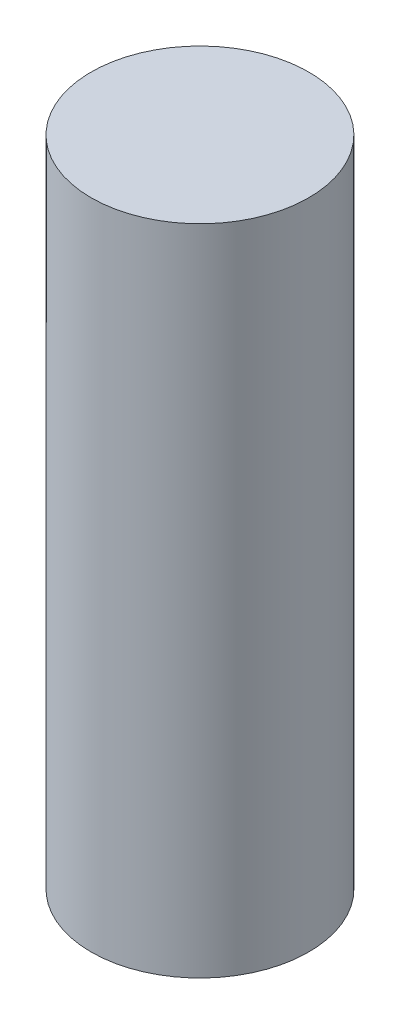
SolidWorks part; units mm, degrees
ref_plane "前视基准面" through (0, 0, 0) normal (0, 0, 1) x (1, 0, 0)
ref_plane "上视基准面" through (0, 0, 0) normal (0, 1, 0) x (1, 0, 0)
ref_plane "右视基准面" through (0, 0, 0) normal (1, 0, 0) x (0, 0, -1)
sketch "草图1" plane through (0, 0, 0) normal (0, 1, 0) x (1, 0, 0)
  circle A0 centre (0, 0) radius 2.5
  dimension "D1" = 5
extrude "凸台-拉伸1" add sketch "草图1" along normal blind 15
